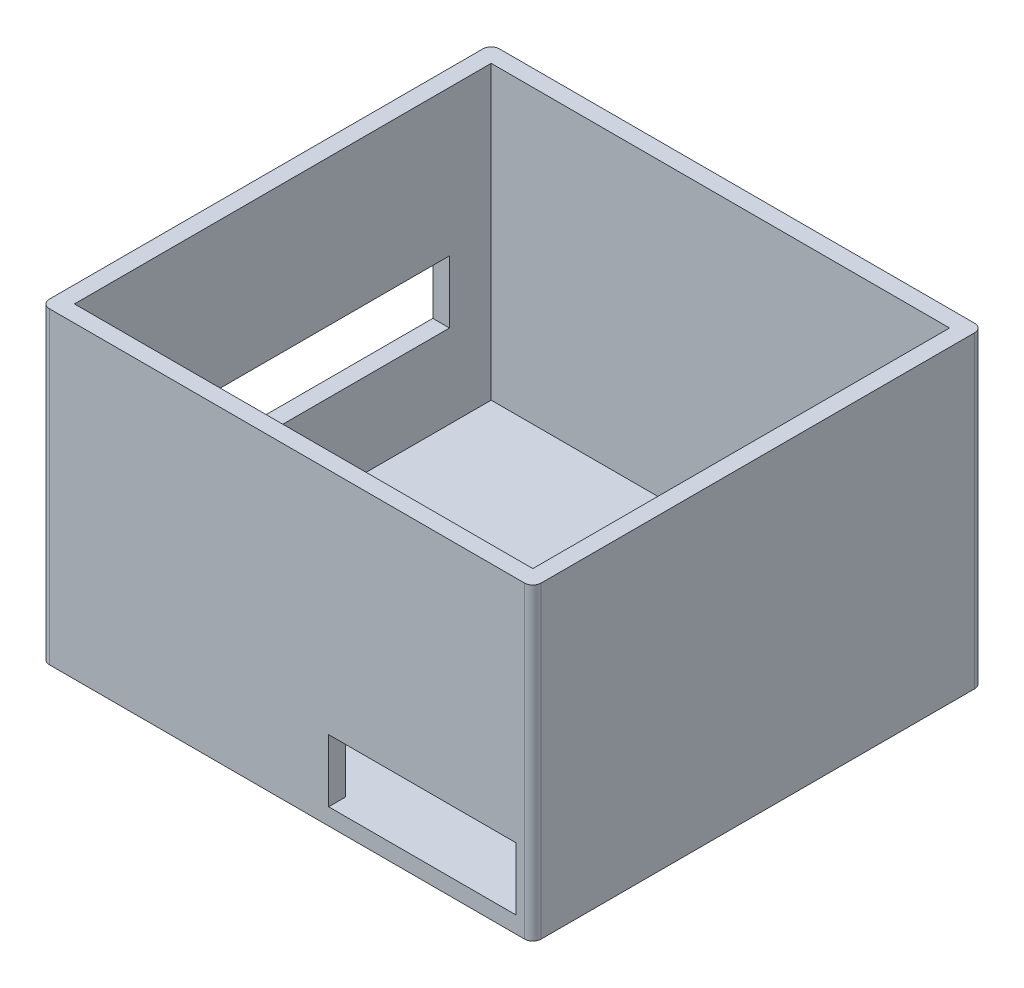
SolidWorks part; units mm, degrees
ref_plane "Front Plane" through (0, 0, 0) normal (0, 0, 1) x (1, 0, 0)
ref_plane "Top Plane" through (0, 0, 0) normal (0, 1, 0) x (1, 0, 0)
ref_plane "Right Plane" through (0, 0, 0) normal (1, 0, 0) x (0, 0, -1)
sketch "Sketch1" plane through (0, 0, 0) normal (0, 1, 0) x (1, 0, 0)
  line L1 (0, 0) -> (118, 0)
  line L2 (0, 0) -> (0, 108)
  line L3 (0, 108) -> (118, 108)
  line L4 (118, 0) -> (118, 108)
  dimension "D1" = 108
  dimension "D2" = 118
extrude "Boss-Extrude1" add sketch "Sketch1" along normal blind 4
sketch "Sketch2" plane through (0, 4, 0) normal (0, 1, 0) x (1, 0, 0)
  line L0 (4, 104) -> (4, 4)
  line L1 (0, 108) -> (118, 108)
  line L2 (0, 108) -> (0, 0)
  line L3 (0, 0) -> (118, 0)
  line L4 (118, 108) -> (118, 0)
  line L5 (4, 4) -> (114, 4)
  line L6 (114, 104) -> (114, 4)
  line L7 (4, 104) -> (114, 104)
  dimension "D1" = 4
extrude "Boss-Extrude2" add sketch "Sketch2" along normal blind 70
sketch "Sketch3" plane through (0, 0, 0) normal (-1, 0, 0) x (0, 0, 1)
  line L0 (-54, 74) -> (-54, 0) construction
  line L1 (-108, 74) -> (0, 74) construction
  line L2 (-108, 0) -> (0, 0) construction
  line L4 (-94, 39) -> (-14, 39)
  line L5 (-94, 39) -> (-94, 24)
  line L6 (-94, 24) -> (-14, 24)
  line L7 (-14, 39) -> (-14, 24)
  line L8 (-94, 39) -> (-14, 24) construction
  line L9 (-94, 24) -> (-14, 39) construction
  point P6 (-54, 31.5)
  dimension "D1" = 80
  dimension "D2" = 15
  dimension "D3" = 24
extrude "Cut-Extrude1" cut sketch "Sketch3" against normal up to surface (4 mm away) up to face at (4, 39, -54)
sketch "Sketch4" plane through (0, 0, 0) normal (0, 0, 1) x (1, 0, 0)
  line L0 (118, 74) -> (118, 0) construction
  line L1 (69, 19) -> (114, 19)
  line L2 (69, 19) -> (69, 4)
  line L3 (69, 4) -> (114, 4)
  line L4 (114, 19) -> (114, 4)
  line L5 (69, 19) -> (114, 4) construction
  line L6 (69, 4) -> (114, 19) construction
  line L7 (0, 0) -> (118, 0) construction
  point P0 (91.5, 11.5)
  dimension "D1" = 45
  dimension "D2" = 4
  dimension "D3" = 4
  dimension "D4" = 15
extrude "Cut-Extrude2" cut sketch "Sketch4" against normal up to surface (4 mm away) up to face at (59, 39, -4)
fillet "Fillet1" radius 2 4 edges at (118, 37, 0) (118, 37, -108) (0, 37, -108) (0, 37, 0)
